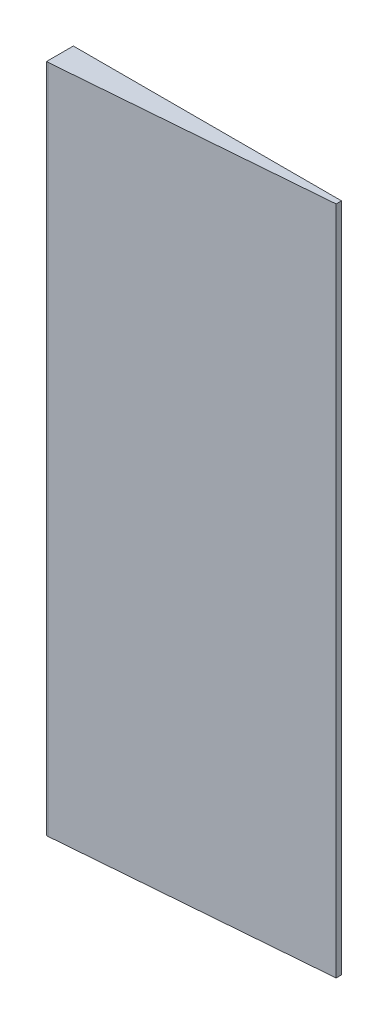
SolidWorks part; units mm, degrees
ref_plane "Front Plane" through (0, 0, 0) normal (0, 0, 1) x (1, 0, 0)
ref_plane "Top Plane" through (0, 0, 0) normal (0, 1, 0) x (1, 0, 0)
ref_plane "Right Plane" through (0, 0, 0) normal (1, 0, 0) x (0, 0, -1)
sketch "Sketch1" plane through (0, 0, 0) normal (0, 0, 1) x (1, 0, 0)
  line L1 (0, 0) -> (-10, 0)
  line L2 (0, 0) -> (0, 25)
  line L3 (0, 25) -> (-10, 25)
  line L4 (-10, 0) -> (-10, 25)
  dimension "D1" = 25
  dimension "D2" = 10
extrude "Boss-Extrude1" add sketch "Sketch1" along normal blind 1 contours L4 L3 L2 L1
chamfer "Chamfer1" distance 0.8 angle 85.4 1 edges at (0, 12.5, 1)
